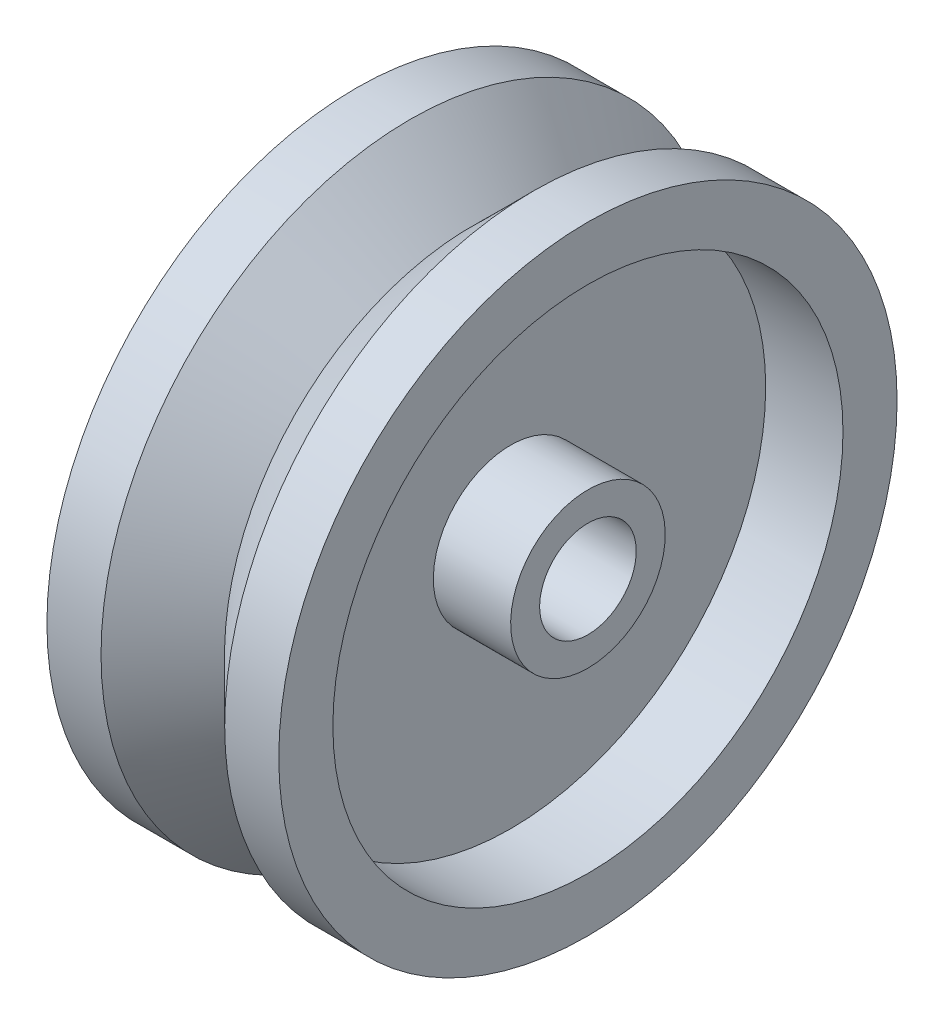
SolidWorks part; units mm, degrees
ref_plane "Front Plane" through (0, 0, 0) normal (0, 0, 1) x (1, 0, 0)
ref_plane "Top Plane" through (0, 0, 0) normal (0, 1, 0) x (1, 0, 0)
ref_plane "Right Plane" through (0, 0, 0) normal (1, 0, 0) x (0, 0, -1)
sketch "Sketch1" plane through (0, 0, 0) normal (0, 0, 1) x (1, 0, 0)
  line L0 (-7.5, 0) -> (7.5, 0) construction
  line L2 (7.5, 3.125) -> (-7.5, 3.125)
  line L4 (2.5, 5) -> (7.5, 5)
  line L5 (-7.5, 3.125) -> (-7.5, 5)
  line L6 (-7.5, 5) -> (-2.5, 5)
  line L7 (7.5, 3.125) -> (7.5, 5)
  line L8 (-4, 20) -> (-0.011, 16)
  line L9 (2.5, 5) -> (2.5, 16.5)
  line L10 (-2.5, 5) -> (-2.5, 16.5)
  line L11 (-2.5, 16.5) -> (-7.5, 16.5)
  line L12 (2.5, 16.5) -> (7.5, 16.5)
  line L13 (-7.5, 16.5) -> (-7.5, 20)
  line L14 (-7.5, 20) -> (-4, 20)
  line L15 (7.5, 20) -> (7.5, 16.5)
  line L16 (4, 20) -> (-0.011, 16)
  line L17 (4, 20) -> (7.5, 20)
  point P4 (0, 0)
  point P14 (0, 5)
  point P21 (0, 20)
  dimension "D1" = 8
  dimension "D2" = 20
  dimension "D3" = 90
  dimension "D4" = 16.5
  dimension "D5" = 5
  dimension "D6" = 3.125
  dimension "D7" = 15
  dimension "D8" = 5
revolve "Revolve1" add sketch "Sketch1" angle 360 mid plane about L0
